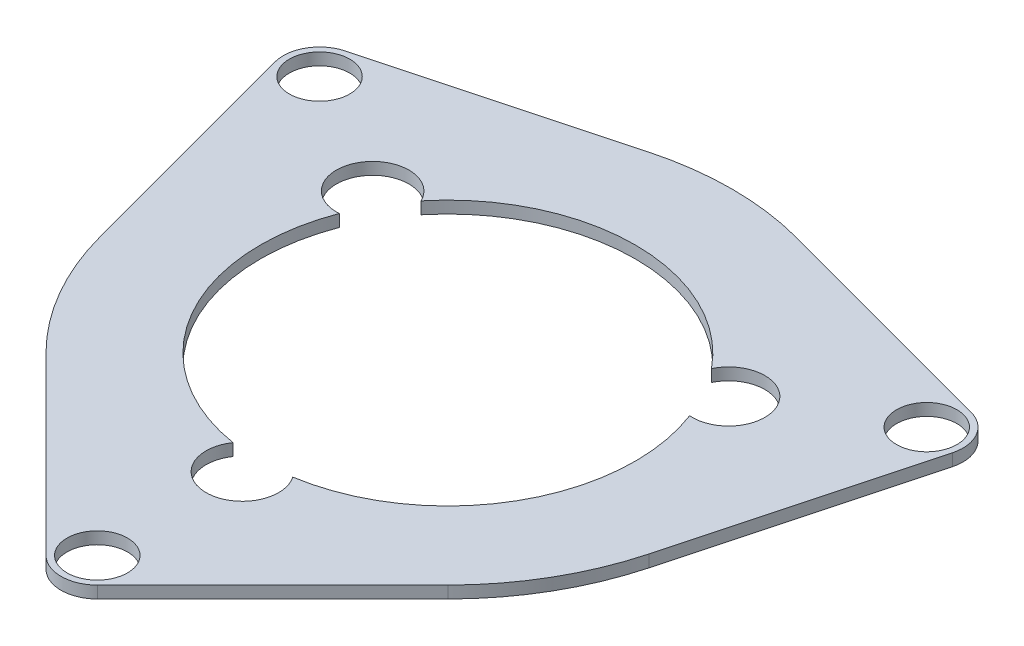
SolidWorks part; units mm, degrees
ref_plane "Face" through (0, 0, 0) normal (0, 0, 1) x (1, 0, 0)
ref_plane "Dessus" through (0, 0, 0) normal (0, 1, 0) x (1, 0, 0)
ref_plane "Droite" through (0, 0, 0) normal (1, 0, 0) x (0, 0, -1)
sketch "Esquisse1" plane through (0, 0, 0) normal (0, 1, 0) x (1, 0, 0)
  line L0 (0, 0) -> (0, 72.1906) construction
  line L1 (-58.6839, 0) -> (64.9715, 0) construction
  line L2 (0, 0) -> (0, -87.6722) construction
  line L3 (-11.3526, -3.0419) -> (-14.0063, 6.8618)
  line L4 (-3.0419, 11.3526) -> (-12.9456, 8.6989)
  line L5 (3.0419, 11.3526) -> (12.9456, 8.6989)
  line L6 (11.3526, -3.0419) -> (14.0063, 6.8618)
  line L7 (8.3107, -8.3107) -> (1.0607, -15.5607)
  line L8 (-8.3107, -8.3107) -> (-1.0607, -15.5607)
  line L9 (-12.5574, 7.25) -> (0, -14.5) construction
  line L10 (0, -14.5) -> (12.5574, 7.25) construction
  line L11 (12.5574, 7.25) -> (-12.5574, 7.25) construction
  line L12 (0, 0) -> (-13.8564, 8) construction
  line L13 (0, 0) -> (13.8564, 8) construction
  arc A0 (-3.0419, 11.3526) -> (3.0419, 11.3526) centre (0, 0) cw
  arc A1 (11.3526, -3.0419) -> (8.3107, -8.3107) centre (0, 0) cw
  arc A2 (-11.3526, -3.0419) -> (-8.3107, -8.3107) centre (0, 0) ccw
  arc A3 (-14.0063, 6.8618) -> (-12.9456, 8.6989) centre (-12.5574, 7.25) cw
  arc A4 (12.9456, 8.6989) -> (14.0063, 6.8618) centre (12.5574, 7.25) cw
  arc A5 (-1.0607, -15.5607) -> (1.0607, -15.5607) centre (0, -14.5) ccw
  circle A6 centre (-12.5574, 7.25) radius 1.25
  circle A7 centre (12.5574, 7.25) radius 1.25
  circle A8 centre (0, -14.5) radius 1.25
  arc A9 (-7.2439, 2.7546) -> (-6.0075, 4.8961) centre (-7.3612, 4.25) cw
  arc A10 (-6.0075, 4.8961) -> (6.0075, 4.8961) centre (0, 0) cw
  arc A11 (6.0075, 4.8961) -> (7.2439, 2.7546) centre (7.3612, 4.25) cw
  arc A12 (7.2439, 2.7546) -> (1.2364, -7.6507) centre (0, 0) cw
  arc A13 (1.2364, -7.6507) -> (-1.2364, -7.6507) centre (0, -8.5) cw
  arc A14 (-1.2364, -7.6507) -> (-7.2439, 2.7546) centre (0, 0) cw
  dimension "D1" = 14.5
  dimension "D4" = 16
  dimension "D6" = 7.75
  dimension "D7" = 2.5
  dimension "D8" = 1.5
  dimension "D2" = 90
  dimension "D3" = 90
  dimension "D5" = 60
  dimension "D9" = 8.5
  dimension "D10" = 8.5
  dimension "D11" = 8.5
extrude "Extrusion1" add sketch "Esquisse1" along normal blind 0.5
